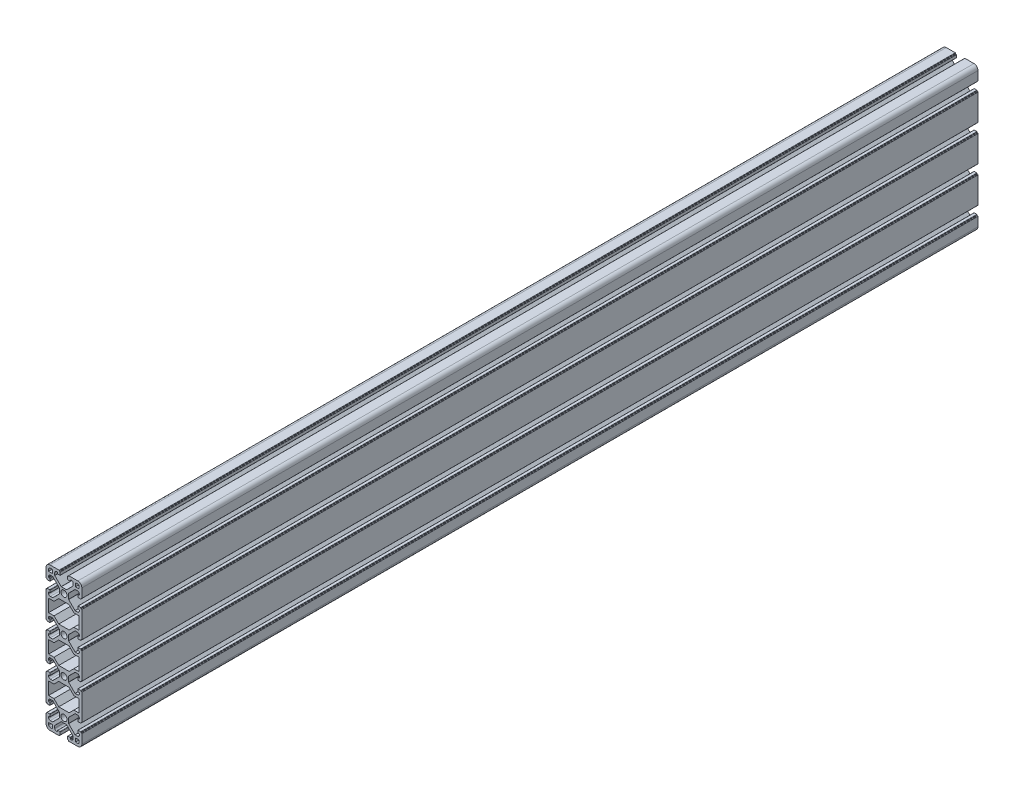
SolidWorks part; units mm, degrees
material "6063 T5"
ref_plane "Спереди" through (0, 0, 0) normal (0, 0, 1) x (1, 0, 0)
ref_plane "Сверху" through (0, 0, 0) normal (0, 1, 0) x (1, 0, 0)
ref_plane "Справа" through (0, 0, 0) normal (1, 0, 0) x (0, 0, -1)
sketch "Эскиз1" plane through (0, 0, 0) normal (0, 0, 1) x (1, 0, 0)
  line L0 (-19.98, 20.5457) -> (20.02, 20.5457) construction
  line L1 (-20, 10.25) -> (-20, 15.5)
  line L2 (-15.5, 20) -> (-10.25, 20)
  line L3 (-35.3695, 20.0843) -> (-35.3695, -99.9157) construction
  line L13 (-13, 13) -> (-17, 13)
  line L14 (-13, 13) -> (-13, 17)
  line L19 (-13, 17) -> (-15.5, 17)
  line L25 (-17, 13) -> (-17, 15.5)
  line L29 (13, 13) -> (17, 13)
  line L30 (17, 13) -> (17, 15.5)
  line L31 (0, 0) -> (0, -40) construction
  line L32 (0, -20) -> (-27.544, -20) construction
  line L33 (-17.1, -27) -> (-17.1, -13)
  line L34 (-17.1, -13) -> (-11.0988, -13)
  line L35 (-11.0988, -13) -> (-5.7988, -7.7)
  line L36 (-5.7988, -7.7) -> (5.7988, -7.7)
  line L37 (11.0988, -13) -> (5.7988, -7.7)
  line L41 (17.1, -13) -> (11.0988, -13)
  line L46 (17.1, -27) -> (17.1, -13)
  line L49 (-17.1, -27) -> (-11.0988, -27)
  line L50 (-11.0988, -27) -> (-5.7988, -32.3)
  line L51 (-20.1159, 24.9491) -> (19.8841, 24.9491) construction
  line L78 (-5.7988, -32.3) -> (5.7988, -32.3)
  line L79 (11.0988, -27) -> (5.7988, -32.3)
  line L84 (17.1, -27) -> (11.0988, -27)
  line L85 (-20, -10.25) -> (-20, -29.75)
  line L86 (-28.8355, 19.0525) -> (-28.8355, -100.9475) construction
  line L87 (-27.3588, -19.7802) -> (-27.3588, -99.7802) construction
  line L88 (20, -10.25) -> (20, -29.75)
  line L89 (13, 17) -> (15.5, 17)
  line L90 (13, 13) -> (13, 17)
  line L103 (15.5, 20) -> (10.25, 20)
  line L108 (20, 10.25) -> (20, 15.5)
  line L109 (20, -50.25) -> (20, -69.75)
  line L114 (-20, -50.25) -> (-20, -69.75)
  line L115 (-11.0988, -67) -> (-5.7988, -72.3)
  line L116 (-5.7988, -72.3) -> (5.7988, -72.3)
  line L117 (11.0988, -67) -> (5.7988, -72.3)
  line L118 (17.1, -67) -> (11.0988, -67)
  line L119 (17.1, -67) -> (17.1, -53)
  line L120 (17.1, -53) -> (11.0988, -53)
  line L121 (11.0988, -53) -> (5.7988, -47.7)
  line L122 (-5.7988, -47.7) -> (5.7988, -47.7)
  line L123 (-11.0988, -53) -> (-5.7988, -47.7)
  line L124 (-17.1, -53) -> (-11.0988, -53)
  line L125 (-17.1, -67) -> (-17.1, -53)
  line L126 (-17.1, -67) -> (-11.0988, -67)
  line L127 (20, -90.25) -> (20, -109.75)
  line L128 (-20, -90.25) -> (-20, -109.75)
  line L129 (-34.6458, 20.0576) -> (-34.6458, -139.9424) construction
  line L130 (-11.0988, -107) -> (-5.7988, -112.3)
  line L131 (-5.7988, -112.3) -> (5.7988, -112.3)
  line L132 (11.0988, -107) -> (5.7988, -112.3)
  line L133 (17.1, -107) -> (11.0988, -107)
  line L134 (17.1, -107) -> (17.1, -93)
  line L135 (17.1, -93) -> (11.0988, -93)
  line L136 (11.0988, -93) -> (5.7988, -87.7)
  line L137 (-5.7988, -87.7) -> (5.7988, -87.7)
  line L138 (-11.0988, -93) -> (-5.7988, -87.7)
  line L139 (-17.1, -93) -> (-11.0988, -93)
  line L140 (-17.1, -107) -> (-17.1, -93)
  line L141 (-17.1, -107) -> (-11.0988, -107)
  line L142 (-20, -10.25) -> (-20, -50.25) construction
  line L143 (-20, -60) -> (-45.2764, -60) construction
  line L144 (-15.5, -140) -> (-10.25, -140)
  line L145 (-20, -130.25) -> (-20, -135.5)
  line L146 (15.5, -140) -> (10.25, -140)
  line L147 (20, -130.25) -> (20, -135.5)
  line L148 (13, -133) -> (13, -137)
  line L149 (13, -137) -> (15.5, -137)
  line L150 (17, -133) -> (17, -135.5)
  line L151 (13, -133) -> (17, -133)
  line L152 (-13, -137) -> (-15.5, -137)
  line L153 (-17, -133) -> (-17, -135.5)
  line L154 (-13, -133) -> (-17, -133)
  line L155 (-13, -133) -> (-13, -137)
  arc A0 (-20, 15.5) -> (-15.5, 20) centre (-15.5, 15.5) cw
  arc A6 (-15.5, 17) -> (-17, 15.5) centre (-15.5, 15.5) ccw
  arc A22 (15.5, 17) -> (17, 15.5) centre (15.5, 15.5) cw
  circle A23 centre (0, 0) radius 3.4
  circle A24 centre (0, -40) radius 3.4
  arc A25 (20, 15.5) -> (15.5, 20) centre (15.5, 15.5) ccw
  circle A26 centre (0, -80) radius 3.4
  circle A27 centre (0, -120) radius 3.4
  arc A28 (-20, -135.5) -> (-15.5, -140) centre (-15.5, -135.5) ccw
  arc A29 (20, -135.5) -> (15.5, -140) centre (15.5, -135.5) cw
  arc A30 (15.5, -137) -> (17, -135.5) centre (15.5, -135.5) ccw
  arc A31 (-15.5, -137) -> (-17, -135.5) centre (-15.5, -135.5) cw
  point P4 (0, 0)
  point P38 (0, -7.7)
  point P42 (-17.1, -20)
  point P45 (0, 0)
  point P48 (17.1, -20)
  point P52 (-20, -20)
  point P53 (20, -20)
  line B0 (-20, 10.25) -> (-20, 5.4)
  line B1 (-19.7, 5.1) -> (-19.3, 5.1)
  line B2 (-19, 4.8) -> (-19, 4.4)
  line B3 (-18.7, 4.1) -> (-15.8, 4.1)
  line B4 (-15.5, 4.4) -> (-15.5, 6.8)
  line B5 (-15.8, 7.1) -> (-16.9, 7.1)
  line B6 (-17.2, 7.4) -> (-17.2, 8.25)
  line B7 (-15.2, 10.25) -> (-12.5743, 10.25)
  line B8 (-12.3621, 10.1621) -> (-5.2879, 3.0879)
  line B9 (-5.2, 2.8757) -> (-5.2, -2.8757)
  line B10 (-5.2, 0) -> (-20, 0) construction
  line B11 (-12.3621, -10.1621) -> (-5.2879, -3.0879)
  line B12 (-15.2, -10.25) -> (-12.5743, -10.25)
  line B13 (-17.2, -7.4) -> (-17.2, -8.25)
  line B14 (-15.8, -7.1) -> (-16.9, -7.1)
  line B15 (-15.5, -4.4) -> (-15.5, -6.8)
  line B16 (-18.7, -4.1) -> (-15.8, -4.1)
  line B17 (-19, -4.8) -> (-19, -4.4)
  line B18 (-19.7, -5.1) -> (-19.3, -5.1)
  line B19 (-20, -10.25) -> (-20, -5.4)
  arc B20 (-15.5, 6.8) -> (-15.8, 7.1) centre (-15.8, 6.8) ccw
  arc B21 (-15.8, 4.1) -> (-15.5, 4.4) centre (-15.8, 4.4) ccw
  arc B22 (-19, 4.4) -> (-18.7, 4.1) centre (-18.7, 4.4) ccw
  arc B23 (-19.3, 5.1) -> (-19, 4.8) centre (-19.3, 4.8) cw
  arc B24 (-20, 5.4) -> (-19.7, 5.1) centre (-19.7, 5.4) ccw
  arc B25 (-5.2879, 3.0879) -> (-5.2, 2.8757) centre (-5.5, 2.8757) cw
  arc B26 (-12.5743, 10.25) -> (-12.3621, 10.1621) centre (-12.5743, 9.95) cw
  arc B27 (-17.2, 8.25) -> (-15.2, 10.25) centre (-15.2, 8.25) cw
  arc B28 (-16.9, 7.1) -> (-17.2, 7.4) centre (-16.9, 7.4) cw
  arc B29 (-16.9, -7.1) -> (-17.2, -7.4) centre (-16.9, -7.4) ccw
  arc B30 (-17.2, -8.25) -> (-15.2, -10.25) centre (-15.2, -8.25) ccw
  arc B31 (-12.5743, -10.25) -> (-12.3621, -10.1621) centre (-12.5743, -9.95) ccw
  arc B32 (-5.2879, -3.0879) -> (-5.2, -2.8757) centre (-5.5, -2.8757) ccw
  arc B33 (-20, -5.4) -> (-19.7, -5.1) centre (-19.7, -5.4) cw
  arc B34 (-19.3, -5.1) -> (-19, -4.8) centre (-19.3, -4.8) ccw
  arc B35 (-19, -4.4) -> (-18.7, -4.1) centre (-18.7, -4.4) cw
  arc B36 (-15.8, -4.1) -> (-15.5, -4.4) centre (-15.8, -4.4) cw
  arc B37 (-15.5, -6.8) -> (-15.8, -7.1) centre (-15.8, -6.8) cw
  line B38 (10.25, 20) -> (5.4, 20)
  line B39 (5.1, 19.7) -> (5.1, 19.3)
  line B40 (4.8, 19) -> (4.4, 19)
  line B41 (4.1, 18.7) -> (4.1, 15.8)
  line B42 (4.4, 15.5) -> (6.8, 15.5)
  line B43 (7.1, 15.8) -> (7.1, 16.9)
  line B44 (7.4, 17.2) -> (8.25, 17.2)
  line B45 (10.25, 15.2) -> (10.25, 12.5743)
  line B46 (10.1621, 12.3621) -> (3.0879, 5.2879)
  line B47 (2.8757, 5.2) -> (-2.8757, 5.2)
  line B48 (0, 5.2) -> (0, 20) construction
  line B49 (-10.1621, 12.3621) -> (-3.0879, 5.2879)
  line B50 (-10.25, 15.2) -> (-10.25, 12.5743)
  line B51 (-7.4, 17.2) -> (-8.25, 17.2)
  line B52 (-7.1, 15.8) -> (-7.1, 16.9)
  line B53 (-4.4, 15.5) -> (-6.8, 15.5)
  line B54 (-4.1, 18.7) -> (-4.1, 15.8)
  line B55 (-4.8, 19) -> (-4.4, 19)
  line B56 (-5.1, 19.7) -> (-5.1, 19.3)
  line B57 (-10.25, 20) -> (-5.4, 20)
  arc B58 (6.8, 15.5) -> (7.1, 15.8) centre (6.8, 15.8) ccw
  arc B59 (4.1, 15.8) -> (4.4, 15.5) centre (4.4, 15.8) ccw
  arc B60 (4.4, 19) -> (4.1, 18.7) centre (4.4, 18.7) ccw
  arc B61 (5.1, 19.3) -> (4.8, 19) centre (4.8, 19.3) cw
  arc B62 (5.4, 20) -> (5.1, 19.7) centre (5.4, 19.7) ccw
  arc B63 (3.0879, 5.2879) -> (2.8757, 5.2) centre (2.8757, 5.5) cw
  arc B64 (10.25, 12.5743) -> (10.1621, 12.3621) centre (9.95, 12.5743) cw
  arc B65 (8.25, 17.2) -> (10.25, 15.2) centre (8.25, 15.2) cw
  arc B66 (7.1, 16.9) -> (7.4, 17.2) centre (7.4, 16.9) cw
  arc B67 (-7.1, 16.9) -> (-7.4, 17.2) centre (-7.4, 16.9) ccw
  arc B68 (-8.25, 17.2) -> (-10.25, 15.2) centre (-8.25, 15.2) ccw
  arc B69 (-10.25, 12.5743) -> (-10.1621, 12.3621) centre (-9.95, 12.5743) ccw
  arc B70 (-3.0879, 5.2879) -> (-2.8757, 5.2) centre (-2.8757, 5.5) ccw
  arc B71 (-5.4, 20) -> (-5.1, 19.7) centre (-5.4, 19.7) cw
  arc B72 (-5.1, 19.3) -> (-4.8, 19) centre (-4.8, 19.3) ccw
  arc B73 (-4.4, 19) -> (-4.1, 18.7) centre (-4.4, 18.7) cw
  arc B74 (-4.1, 15.8) -> (-4.4, 15.5) centre (-4.4, 15.8) cw
  arc B75 (-6.8, 15.5) -> (-7.1, 15.8) centre (-6.8, 15.8) cw
  line B76 (20, -10.25) -> (20, -5.4)
  line B77 (19.7, -5.1) -> (19.3, -5.1)
  line B78 (19, -4.8) -> (19, -4.4)
  line B79 (18.7, -4.1) -> (15.8, -4.1)
  line B80 (15.5, -4.4) -> (15.5, -6.8)
  line B81 (15.8, -7.1) -> (16.9, -7.1)
  line B82 (17.2, -7.4) -> (17.2, -8.25)
  line B83 (15.2, -10.25) -> (12.5743, -10.25)
  line B84 (12.3621, -10.1621) -> (5.2879, -3.0879)
  line B85 (5.2, -2.8757) -> (5.2, 2.8757)
  line B86 (5.2, 0) -> (20, 0) construction
  line B87 (12.3621, 10.1621) -> (5.2879, 3.0879)
  line B88 (15.2, 10.25) -> (12.5743, 10.25)
  line B89 (17.2, 7.4) -> (17.2, 8.25)
  line B90 (15.8, 7.1) -> (16.9, 7.1)
  line B91 (15.5, 4.4) -> (15.5, 6.8)
  line B92 (18.7, 4.1) -> (15.8, 4.1)
  line B93 (19, 4.8) -> (19, 4.4)
  line B94 (19.7, 5.1) -> (19.3, 5.1)
  line B95 (20, 10.25) -> (20, 5.4)
  arc B96 (15.5, -6.8) -> (15.8, -7.1) centre (15.8, -6.8) ccw
  arc B97 (15.8, -4.1) -> (15.5, -4.4) centre (15.8, -4.4) ccw
  arc B98 (19, -4.4) -> (18.7, -4.1) centre (18.7, -4.4) ccw
  arc B99 (19.3, -5.1) -> (19, -4.8) centre (19.3, -4.8) cw
  arc B100 (20, -5.4) -> (19.7, -5.1) centre (19.7, -5.4) ccw
  arc B101 (5.2879, -3.0879) -> (5.2, -2.8757) centre (5.5, -2.8757) cw
  arc B102 (12.5743, -10.25) -> (12.3621, -10.1621) centre (12.5743, -9.95) cw
  arc B103 (17.2, -8.25) -> (15.2, -10.25) centre (15.2, -8.25) cw
  arc B104 (16.9, -7.1) -> (17.2, -7.4) centre (16.9, -7.4) cw
  arc B105 (16.9, 7.1) -> (17.2, 7.4) centre (16.9, 7.4) ccw
  arc B106 (17.2, 8.25) -> (15.2, 10.25) centre (15.2, 8.25) ccw
  arc B107 (12.5743, 10.25) -> (12.3621, 10.1621) centre (12.5743, 9.95) ccw
  arc B108 (5.2879, 3.0879) -> (5.2, 2.8757) centre (5.5, 2.8757) ccw
  arc B109 (20, 5.4) -> (19.7, 5.1) centre (19.7, 5.4) cw
  arc B110 (19.3, 5.1) -> (19, 4.8) centre (19.3, 4.8) ccw
  arc B111 (19, 4.4) -> (18.7, 4.1) centre (18.7, 4.4) cw
  arc B112 (15.8, 4.1) -> (15.5, 4.4) centre (15.8, 4.4) cw
  arc B113 (15.5, 6.8) -> (15.8, 7.1) centre (15.8, 6.8) cw
  line B114 (-20, -29.75) -> (-20, -34.6)
  line B115 (-19.7, -34.9) -> (-19.3, -34.9)
  line B116 (-19, -35.2) -> (-19, -35.6)
  line B117 (-18.7, -35.9) -> (-15.8, -35.9)
  line B118 (-15.5, -35.6) -> (-15.5, -33.2)
  line B119 (-15.8, -32.9) -> (-16.9, -32.9)
  line B120 (-17.2, -32.6) -> (-17.2, -31.75)
  line B121 (-15.2, -29.75) -> (-12.5743, -29.75)
  line B122 (-12.3621, -29.8379) -> (-5.2879, -36.9121)
  line B123 (-5.2, -37.1243) -> (-5.2, -42.8757)
  line B124 (-5.2, -40) -> (-20, -40) construction
  line B125 (-12.3621, -50.1621) -> (-5.2879, -43.0879)
  line B126 (-15.2, -50.25) -> (-12.5743, -50.25)
  line B127 (-17.2, -47.4) -> (-17.2, -48.25)
  line B128 (-15.8, -47.1) -> (-16.9, -47.1)
  line B129 (-15.5, -44.4) -> (-15.5, -46.8)
  line B130 (-18.7, -44.1) -> (-15.8, -44.1)
  line B131 (-19, -44.8) -> (-19, -44.4)
  line B132 (-19.7, -45.1) -> (-19.3, -45.1)
  line B133 (-20, -50.25) -> (-20, -45.4)
  arc B134 (-15.5, -33.2) -> (-15.8, -32.9) centre (-15.8, -33.2) ccw
  arc B135 (-15.8, -35.9) -> (-15.5, -35.6) centre (-15.8, -35.6) ccw
  arc B136 (-19, -35.6) -> (-18.7, -35.9) centre (-18.7, -35.6) ccw
  arc B137 (-19.3, -34.9) -> (-19, -35.2) centre (-19.3, -35.2) cw
  arc B138 (-20, -34.6) -> (-19.7, -34.9) centre (-19.7, -34.6) ccw
  arc B139 (-5.2879, -36.9121) -> (-5.2, -37.1243) centre (-5.5, -37.1243) cw
  arc B140 (-12.5743, -29.75) -> (-12.3621, -29.8379) centre (-12.5743, -30.05) cw
  arc B141 (-17.2, -31.75) -> (-15.2, -29.75) centre (-15.2, -31.75) cw
  arc B142 (-16.9, -32.9) -> (-17.2, -32.6) centre (-16.9, -32.6) cw
  arc B143 (-16.9, -47.1) -> (-17.2, -47.4) centre (-16.9, -47.4) ccw
  arc B144 (-17.2, -48.25) -> (-15.2, -50.25) centre (-15.2, -48.25) ccw
  arc B145 (-12.5743, -50.25) -> (-12.3621, -50.1621) centre (-12.5743, -49.95) ccw
  arc B146 (-5.2879, -43.0879) -> (-5.2, -42.8757) centre (-5.5, -42.8757) ccw
  arc B147 (-20, -45.4) -> (-19.7, -45.1) centre (-19.7, -45.4) cw
  arc B148 (-19.3, -45.1) -> (-19, -44.8) centre (-19.3, -44.8) ccw
  arc B149 (-19, -44.4) -> (-18.7, -44.1) centre (-18.7, -44.4) cw
  arc B150 (-15.8, -44.1) -> (-15.5, -44.4) centre (-15.8, -44.4) cw
  arc B151 (-15.5, -46.8) -> (-15.8, -47.1) centre (-15.8, -46.8) cw
  line B152 (20, -50.25) -> (20, -45.4)
  line B153 (19.7, -45.1) -> (19.3, -45.1)
  line B154 (19, -44.8) -> (19, -44.4)
  line B155 (18.7, -44.1) -> (15.8, -44.1)
  line B156 (15.5, -44.4) -> (15.5, -46.8)
  line B157 (15.8, -47.1) -> (16.9, -47.1)
  line B158 (17.2, -47.4) -> (17.2, -48.25)
  line B159 (15.2, -50.25) -> (12.5743, -50.25)
  line B160 (12.3621, -50.1621) -> (5.2879, -43.0879)
  line B161 (5.2, -42.8757) -> (5.2, -37.1243)
  line B162 (5.2, -40) -> (20, -40) construction
  line B163 (12.3621, -29.8379) -> (5.2879, -36.9121)
  line B164 (15.2, -29.75) -> (12.5743, -29.75)
  line B165 (17.2, -32.6) -> (17.2, -31.75)
  line B166 (15.8, -32.9) -> (16.9, -32.9)
  line B167 (15.5, -35.6) -> (15.5, -33.2)
  line B168 (18.7, -35.9) -> (15.8, -35.9)
  line B169 (19, -35.2) -> (19, -35.6)
  line B170 (19.7, -34.9) -> (19.3, -34.9)
  line B171 (20, -29.75) -> (20, -34.6)
  arc B172 (15.5, -46.8) -> (15.8, -47.1) centre (15.8, -46.8) ccw
  arc B173 (15.8, -44.1) -> (15.5, -44.4) centre (15.8, -44.4) ccw
  arc B174 (19, -44.4) -> (18.7, -44.1) centre (18.7, -44.4) ccw
  arc B175 (19.3, -45.1) -> (19, -44.8) centre (19.3, -44.8) cw
  arc B176 (20, -45.4) -> (19.7, -45.1) centre (19.7, -45.4) ccw
  arc B177 (5.2879, -43.0879) -> (5.2, -42.8757) centre (5.5, -42.8757) cw
  arc B178 (12.5743, -50.25) -> (12.3621, -50.1621) centre (12.5743, -49.95) cw
  arc B179 (17.2, -48.25) -> (15.2, -50.25) centre (15.2, -48.25) cw
  arc B180 (16.9, -47.1) -> (17.2, -47.4) centre (16.9, -47.4) cw
  arc B181 (16.9, -32.9) -> (17.2, -32.6) centre (16.9, -32.6) ccw
  arc B182 (17.2, -31.75) -> (15.2, -29.75) centre (15.2, -31.75) ccw
  arc B183 (12.5743, -29.75) -> (12.3621, -29.8379) centre (12.5743, -30.05) ccw
  arc B184 (5.2879, -36.9121) -> (5.2, -37.1243) centre (5.5, -37.1243) ccw
  arc B185 (20, -34.6) -> (19.7, -34.9) centre (19.7, -34.6) cw
  arc B186 (19.3, -34.9) -> (19, -35.2) centre (19.3, -35.2) ccw
  arc B187 (19, -35.6) -> (18.7, -35.9) centre (18.7, -35.6) cw
  arc B188 (15.8, -35.9) -> (15.5, -35.6) centre (15.8, -35.6) cw
  arc B189 (15.5, -33.2) -> (15.8, -32.9) centre (15.8, -33.2) cw
  line B190 (-20, -69.75) -> (-20, -74.6)
  line B191 (-19.7, -74.9) -> (-19.3, -74.9)
  line B192 (-19, -75.2) -> (-19, -75.6)
  line B193 (-18.7, -75.9) -> (-15.8, -75.9)
  line B194 (-15.5, -75.6) -> (-15.5, -73.2)
  line B195 (-15.8, -72.9) -> (-16.9, -72.9)
  line B196 (-17.2, -72.6) -> (-17.2, -71.75)
  line B197 (-15.2, -69.75) -> (-12.5743, -69.75)
  line B198 (-12.3621, -69.8379) -> (-5.2879, -76.9121)
  line B199 (-5.2, -77.1243) -> (-5.2, -82.8757)
  line B200 (-5.2, -80) -> (-20, -80) construction
  line B201 (-12.3621, -90.1621) -> (-5.2879, -83.0879)
  line B202 (-15.2, -90.25) -> (-12.5743, -90.25)
  line B203 (-17.2, -87.4) -> (-17.2, -88.25)
  line B204 (-15.8, -87.1) -> (-16.9, -87.1)
  line B205 (-15.5, -84.4) -> (-15.5, -86.8)
  line B206 (-18.7, -84.1) -> (-15.8, -84.1)
  line B207 (-19, -84.8) -> (-19, -84.4)
  line B208 (-19.7, -85.1) -> (-19.3, -85.1)
  line B209 (-20, -90.25) -> (-20, -85.4)
  arc B210 (-15.5, -73.2) -> (-15.8, -72.9) centre (-15.8, -73.2) ccw
  arc B211 (-15.8, -75.9) -> (-15.5, -75.6) centre (-15.8, -75.6) ccw
  arc B212 (-19, -75.6) -> (-18.7, -75.9) centre (-18.7, -75.6) ccw
  arc B213 (-19.3, -74.9) -> (-19, -75.2) centre (-19.3, -75.2) cw
  arc B214 (-20, -74.6) -> (-19.7, -74.9) centre (-19.7, -74.6) ccw
  arc B215 (-5.2879, -76.9121) -> (-5.2, -77.1243) centre (-5.5, -77.1243) cw
  arc B216 (-12.5743, -69.75) -> (-12.3621, -69.8379) centre (-12.5743, -70.05) cw
  arc B217 (-17.2, -71.75) -> (-15.2, -69.75) centre (-15.2, -71.75) cw
  arc B218 (-16.9, -72.9) -> (-17.2, -72.6) centre (-16.9, -72.6) cw
  arc B219 (-16.9, -87.1) -> (-17.2, -87.4) centre (-16.9, -87.4) ccw
  arc B220 (-17.2, -88.25) -> (-15.2, -90.25) centre (-15.2, -88.25) ccw
  arc B221 (-12.5743, -90.25) -> (-12.3621, -90.1621) centre (-12.5743, -89.95) ccw
  arc B222 (-5.2879, -83.0879) -> (-5.2, -82.8757) centre (-5.5, -82.8757) ccw
  arc B223 (-20, -85.4) -> (-19.7, -85.1) centre (-19.7, -85.4) cw
  arc B224 (-19.3, -85.1) -> (-19, -84.8) centre (-19.3, -84.8) ccw
  arc B225 (-19, -84.4) -> (-18.7, -84.1) centre (-18.7, -84.4) cw
  arc B226 (-15.8, -84.1) -> (-15.5, -84.4) centre (-15.8, -84.4) cw
  arc B227 (-15.5, -86.8) -> (-15.8, -87.1) centre (-15.8, -86.8) cw
  line B228 (20, -90.25) -> (20, -85.4)
  line B229 (19.7, -85.1) -> (19.3, -85.1)
  line B230 (19, -84.8) -> (19, -84.4)
  line B231 (18.7, -84.1) -> (15.8, -84.1)
  line B232 (15.5, -84.4) -> (15.5, -86.8)
  line B233 (15.8, -87.1) -> (16.9, -87.1)
  line B234 (17.2, -87.4) -> (17.2, -88.25)
  line B235 (15.2, -90.25) -> (12.5743, -90.25)
  line B236 (12.3621, -90.1621) -> (5.2879, -83.0879)
  line B237 (5.2, -82.8757) -> (5.2, -77.1243)
  line B238 (5.2, -80) -> (20, -80) construction
  line B239 (12.3621, -69.8379) -> (5.2879, -76.9121)
  line B240 (15.2, -69.75) -> (12.5743, -69.75)
  line B241 (17.2, -72.6) -> (17.2, -71.75)
  line B242 (15.8, -72.9) -> (16.9, -72.9)
  line B243 (15.5, -75.6) -> (15.5, -73.2)
  line B244 (18.7, -75.9) -> (15.8, -75.9)
  line B245 (19, -75.2) -> (19, -75.6)
  line B246 (19.7, -74.9) -> (19.3, -74.9)
  line B247 (20, -69.75) -> (20, -74.6)
  arc B248 (15.5, -86.8) -> (15.8, -87.1) centre (15.8, -86.8) ccw
  arc B249 (15.8, -84.1) -> (15.5, -84.4) centre (15.8, -84.4) ccw
  arc B250 (19, -84.4) -> (18.7, -84.1) centre (18.7, -84.4) ccw
  arc B251 (19.3, -85.1) -> (19, -84.8) centre (19.3, -84.8) cw
  arc B252 (20, -85.4) -> (19.7, -85.1) centre (19.7, -85.4) ccw
  arc B253 (5.2879, -83.0879) -> (5.2, -82.8757) centre (5.5, -82.8757) cw
  arc B254 (12.5743, -90.25) -> (12.3621, -90.1621) centre (12.5743, -89.95) cw
  arc B255 (17.2, -88.25) -> (15.2, -90.25) centre (15.2, -88.25) cw
  arc B256 (16.9, -87.1) -> (17.2, -87.4) centre (16.9, -87.4) cw
  arc B257 (16.9, -72.9) -> (17.2, -72.6) centre (16.9, -72.6) ccw
  arc B258 (17.2, -71.75) -> (15.2, -69.75) centre (15.2, -71.75) ccw
  arc B259 (12.5743, -69.75) -> (12.3621, -69.8379) centre (12.5743, -70.05) ccw
  arc B260 (5.2879, -76.9121) -> (5.2, -77.1243) centre (5.5, -77.1243) ccw
  arc B261 (20, -74.6) -> (19.7, -74.9) centre (19.7, -74.6) cw
  arc B262 (19.3, -74.9) -> (19, -75.2) centre (19.3, -75.2) ccw
  arc B263 (19, -75.6) -> (18.7, -75.9) centre (18.7, -75.6) cw
  arc B264 (15.8, -75.9) -> (15.5, -75.6) centre (15.8, -75.6) cw
  arc B265 (15.5, -73.2) -> (15.8, -72.9) centre (15.8, -73.2) cw
  line B266 (-20, -130.25) -> (-20, -125.4)
  line B267 (-19.7, -125.1) -> (-19.3, -125.1)
  line B268 (-19, -124.8) -> (-19, -124.4)
  line B269 (-18.7, -124.1) -> (-15.8, -124.1)
  line B270 (-15.5, -124.4) -> (-15.5, -126.8)
  line B271 (-15.8, -127.1) -> (-16.9, -127.1)
  line B272 (-17.2, -127.4) -> (-17.2, -128.25)
  line B273 (-15.2, -130.25) -> (-12.5743, -130.25)
  line B274 (-12.3621, -130.1621) -> (-5.2879, -123.0879)
  line B275 (-5.2, -122.8757) -> (-5.2, -117.1243)
  line B276 (-5.2, -120) -> (-20, -120) construction
  line B277 (-12.3621, -109.8379) -> (-5.2879, -116.9121)
  line B278 (-15.2, -109.75) -> (-12.5743, -109.75)
  line B279 (-17.2, -112.6) -> (-17.2, -111.75)
  line B280 (-15.8, -112.9) -> (-16.9, -112.9)
  line B281 (-15.5, -115.6) -> (-15.5, -113.2)
  line B282 (-18.7, -115.9) -> (-15.8, -115.9)
  line B283 (-19, -115.2) -> (-19, -115.6)
  line B284 (-19.7, -114.9) -> (-19.3, -114.9)
  line B285 (-20, -109.75) -> (-20, -114.6)
  arc B286 (-15.5, -126.8) -> (-15.8, -127.1) centre (-15.8, -126.8) cw
  arc B287 (-15.8, -124.1) -> (-15.5, -124.4) centre (-15.8, -124.4) cw
  arc B288 (-19, -124.4) -> (-18.7, -124.1) centre (-18.7, -124.4) cw
  arc B289 (-19.3, -125.1) -> (-19, -124.8) centre (-19.3, -124.8) ccw
  arc B290 (-20, -125.4) -> (-19.7, -125.1) centre (-19.7, -125.4) cw
  arc B291 (-5.2879, -123.0879) -> (-5.2, -122.8757) centre (-5.5, -122.8757) ccw
  arc B292 (-12.5743, -130.25) -> (-12.3621, -130.1621) centre (-12.5743, -129.95) ccw
  arc B293 (-17.2, -128.25) -> (-15.2, -130.25) centre (-15.2, -128.25) ccw
  arc B294 (-16.9, -127.1) -> (-17.2, -127.4) centre (-16.9, -127.4) ccw
  arc B295 (-16.9, -112.9) -> (-17.2, -112.6) centre (-16.9, -112.6) cw
  arc B296 (-17.2, -111.75) -> (-15.2, -109.75) centre (-15.2, -111.75) cw
  arc B297 (-12.5743, -109.75) -> (-12.3621, -109.8379) centre (-12.5743, -110.05) cw
  arc B298 (-5.2879, -116.9121) -> (-5.2, -117.1243) centre (-5.5, -117.1243) cw
  arc B299 (-20, -114.6) -> (-19.7, -114.9) centre (-19.7, -114.6) ccw
  arc B300 (-19.3, -114.9) -> (-19, -115.2) centre (-19.3, -115.2) cw
  arc B301 (-19, -115.6) -> (-18.7, -115.9) centre (-18.7, -115.6) ccw
  arc B302 (-15.8, -115.9) -> (-15.5, -115.6) centre (-15.8, -115.6) ccw
  arc B303 (-15.5, -113.2) -> (-15.8, -112.9) centre (-15.8, -113.2) ccw
  line B304 (10.25, -140) -> (5.4, -140)
  line B305 (5.1, -139.7) -> (5.1, -139.3)
  line B306 (4.8, -139) -> (4.4, -139)
  line B307 (4.1, -138.7) -> (4.1, -135.8)
  line B308 (4.4, -135.5) -> (6.8, -135.5)
  line B309 (7.1, -135.8) -> (7.1, -136.9)
  line B310 (7.4, -137.2) -> (8.25, -137.2)
  line B311 (10.25, -135.2) -> (10.25, -132.5743)
  line B312 (10.1621, -132.3621) -> (3.0879, -125.2879)
  line B313 (2.8757, -125.2) -> (-2.8757, -125.2)
  line B314 (0, -125.2) -> (0, -140) construction
  line B315 (-10.1621, -132.3621) -> (-3.0879, -125.2879)
  line B316 (-10.25, -135.2) -> (-10.25, -132.5743)
  line B317 (-7.4, -137.2) -> (-8.25, -137.2)
  line B318 (-7.1, -135.8) -> (-7.1, -136.9)
  line B319 (-4.4, -135.5) -> (-6.8, -135.5)
  line B320 (-4.1, -138.7) -> (-4.1, -135.8)
  line B321 (-4.8, -139) -> (-4.4, -139)
  line B322 (-5.1, -139.7) -> (-5.1, -139.3)
  line B323 (-10.25, -140) -> (-5.4, -140)
  arc B324 (6.8, -135.5) -> (7.1, -135.8) centre (6.8, -135.8) cw
  arc B325 (4.1, -135.8) -> (4.4, -135.5) centre (4.4, -135.8) cw
  arc B326 (4.4, -139) -> (4.1, -138.7) centre (4.4, -138.7) cw
  arc B327 (5.1, -139.3) -> (4.8, -139) centre (4.8, -139.3) ccw
  arc B328 (5.4, -140) -> (5.1, -139.7) centre (5.4, -139.7) cw
  arc B329 (3.0879, -125.2879) -> (2.8757, -125.2) centre (2.8757, -125.5) ccw
  arc B330 (10.25, -132.5743) -> (10.1621, -132.3621) centre (9.95, -132.5743) ccw
  arc B331 (8.25, -137.2) -> (10.25, -135.2) centre (8.25, -135.2) ccw
  arc B332 (7.1, -136.9) -> (7.4, -137.2) centre (7.4, -136.9) ccw
  arc B333 (-7.1, -136.9) -> (-7.4, -137.2) centre (-7.4, -136.9) cw
  arc B334 (-8.25, -137.2) -> (-10.25, -135.2) centre (-8.25, -135.2) cw
  arc B335 (-10.25, -132.5743) -> (-10.1621, -132.3621) centre (-9.95, -132.5743) cw
  arc B336 (-3.0879, -125.2879) -> (-2.8757, -125.2) centre (-2.8757, -125.5) cw
  arc B337 (-5.4, -140) -> (-5.1, -139.7) centre (-5.4, -139.7) ccw
  arc B338 (-5.1, -139.3) -> (-4.8, -139) centre (-4.8, -139.3) cw
  arc B339 (-4.4, -139) -> (-4.1, -138.7) centre (-4.4, -138.7) ccw
  arc B340 (-4.1, -135.8) -> (-4.4, -135.5) centre (-4.4, -135.8) ccw
  arc B341 (-6.8, -135.5) -> (-7.1, -135.8) centre (-6.8, -135.8) ccw
  line B342 (20, -109.75) -> (20, -114.6)
  line B343 (19.7, -114.9) -> (19.3, -114.9)
  line B344 (19, -115.2) -> (19, -115.6)
  line B345 (18.7, -115.9) -> (15.8, -115.9)
  line B346 (15.5, -115.6) -> (15.5, -113.2)
  line B347 (15.8, -112.9) -> (16.9, -112.9)
  line B348 (17.2, -112.6) -> (17.2, -111.75)
  line B349 (15.2, -109.75) -> (12.5743, -109.75)
  line B350 (12.3621, -109.8379) -> (5.2879, -116.9121)
  line B351 (5.2, -117.1243) -> (5.2, -122.8757)
  line B352 (5.2, -120) -> (20, -120) construction
  line B353 (12.3621, -130.1621) -> (5.2879, -123.0879)
  line B354 (15.2, -130.25) -> (12.5743, -130.25)
  line B355 (17.2, -127.4) -> (17.2, -128.25)
  line B356 (15.8, -127.1) -> (16.9, -127.1)
  line B357 (15.5, -124.4) -> (15.5, -126.8)
  line B358 (18.7, -124.1) -> (15.8, -124.1)
  line B359 (19, -124.8) -> (19, -124.4)
  line B360 (19.7, -125.1) -> (19.3, -125.1)
  line B361 (20, -130.25) -> (20, -125.4)
  arc B362 (15.5, -113.2) -> (15.8, -112.9) centre (15.8, -113.2) cw
  arc B363 (15.8, -115.9) -> (15.5, -115.6) centre (15.8, -115.6) cw
  arc B364 (19, -115.6) -> (18.7, -115.9) centre (18.7, -115.6) cw
  arc B365 (19.3, -114.9) -> (19, -115.2) centre (19.3, -115.2) ccw
  arc B366 (20, -114.6) -> (19.7, -114.9) centre (19.7, -114.6) cw
  arc B367 (5.2879, -116.9121) -> (5.2, -117.1243) centre (5.5, -117.1243) ccw
  arc B368 (12.5743, -109.75) -> (12.3621, -109.8379) centre (12.5743, -110.05) ccw
  arc B369 (17.2, -111.75) -> (15.2, -109.75) centre (15.2, -111.75) ccw
  arc B370 (16.9, -112.9) -> (17.2, -112.6) centre (16.9, -112.6) ccw
  arc B371 (16.9, -127.1) -> (17.2, -127.4) centre (16.9, -127.4) cw
  arc B372 (17.2, -128.25) -> (15.2, -130.25) centre (15.2, -128.25) cw
  arc B373 (12.5743, -130.25) -> (12.3621, -130.1621) centre (12.5743, -129.95) cw
  arc B374 (5.2879, -123.0879) -> (5.2, -122.8757) centre (5.5, -122.8757) cw
  arc B375 (20, -125.4) -> (19.7, -125.1) centre (19.7, -125.4) ccw
  arc B376 (19.3, -125.1) -> (19, -124.8) centre (19.3, -124.8) cw
  arc B377 (19, -124.4) -> (18.7, -124.1) centre (18.7, -124.4) ccw
  arc B378 (15.8, -124.1) -> (15.5, -124.4) centre (15.8, -124.4) ccw
  arc B379 (15.5, -126.8) -> (15.8, -127.1) centre (15.8, -126.8) ccw
  dimension "D12" = 12.3
  dimension "D13" = 2.9
  dimension "D3" = 120
  dimension "D5" = 1.5
  dimension "D6" = 4
  dimension "D4" = 4.5
  dimension "D8" = 6.8
  dimension "D7" = 40
  dimension "D9" = 20
  dimension "D10" = 2.9
  dimension "D11" = 7
  dimension "D14" = 3
  dimension "D15" = 40
  dimension "D16" = 160
  dimension "D17" = 40
  dimension "D26" = 160
sketch_block_instance "Блок1-1"
sketch_block "Блок1" parameters "D7"=0.3, "D8"=0.3, "D12"=2, "D1"=14.8, "D2"=4.5, "D3"=8.2, "D4"=20.5, "D5"=10.2, "D6"=135, "D9"=1, "D10"=3, "D11"=1.7
sketch_block_instance "Блок1-2"
sketch_block_instance "Блок1-3"
sketch_block_instance "Блок1-5"
sketch_block_instance "Блок1-6"
sketch_block_instance "Блок1-7"
sketch_block_instance "Блок1-8"
sketch_block_instance "Блок1-12"
sketch_block_instance "Блок1-13"
sketch_block_instance "Блок1-14"
extrude "Бобышка-Вытянуть1" add sketch "Эскиз1" along normal blind 1000 contours B357 B379 B356 B371 B355 B372 B354 B373 B353 B374 B351 B367 B350 B368 B349 B369 B348 B370 B347 B362 B346 B363 B345 B364 B344 B365 B343 B366 B342 L127 B228 B252 B229 B251 B230 B250 B231 B249 B232 B248 B233 B256 B234 B255 B235 B254 B236 B253 B237 B260 B239
